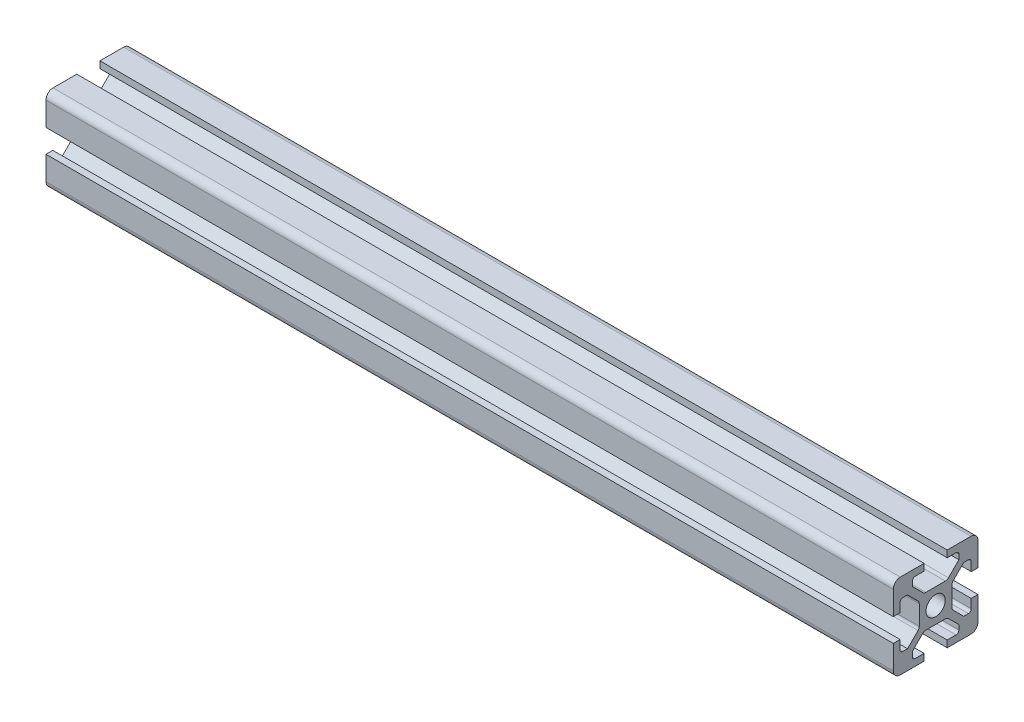
SolidWorks part; units mm, degrees
ref_plane "Front Plane" through (0, 0, 0) normal (0, 0, 1) x (1, 0, 0)
ref_plane "Top Plane" through (0, 0, 0) normal (0, 1, 0) x (1, 0, 0)
ref_plane "Right Plane" through (0, 0, 0) normal (1, 0, 0) x (0, 0, -1)
sketch "Sketch1" plane through (0, 0, 0) normal (1, 0, 0) x (0, 0, -1)
  line L0 (10.9, 0) -> (10.9, 2.4)
  line L1 (0, 0) -> (10.9, 0)
  line L2 (0, 0) -> (0, 10.9)
  line L3 (0, 30) -> (10.9, 30)
  line L4 (30, 0) -> (30, 10.9)
  line L5 (19.1, 0) -> (19.1, 2.4)
  line L6 (0, 10.9) -> (2.4, 10.9)
  line L7 (0, 19.1) -> (2.4, 19.1)
  line L8 (10.9, 30) -> (10.9, 27.6)
  line L9 (19.1, 30) -> (19.1, 27.6)
  line L10 (30, 19.1) -> (27.6, 19.1)
  line L11 (27.6, 10.9) -> (30, 10.9)
  line L12 (24.95, 23.25) -> (27.6, 23.25)
  line L18 (6.75, 2.4) -> (10.9, 2.4)
  line L19 (27.6, 6.75) -> (27.6, 10.9)
  line L20 (2.4, 6.75) -> (2.4, 10.9)
  line L21 (6.75, 27.6) -> (10.9, 27.6)
  line L22 (19.1, 2.4) -> (23.25, 2.4)
  line L23 (27.6, 19.1) -> (27.6, 23.25)
  line L24 (2.4, 19.1) -> (2.4, 23.25)
  line L25 (19.1, 27.6) -> (23.25, 27.6)
  line L26 (19.1, 20.8) -> (10.9, 20.8)
  line L29 (5.05, 6.75) -> (2.4, 6.75)
  line L31 (2.4, 23.25) -> (5.05, 23.25)
  line L34 (6.75, 24.95) -> (6.75, 27.6)
  line L40 (23.25, 2.4) -> (23.25, 5.05)
  line L43 (9.2, 10.9) -> (9.2, 19.1)
  line L44 (19.1, 9.2) -> (10.9, 9.2)
  line L45 (20.8, 10.9) -> (20.8, 19.1)
  line L46 (24.95, 6.75) -> (20.8, 10.9)
  line L47 (19.1, 9.2) -> (23.25, 5.05)
  line L48 (20.8, 19.1) -> (24.95, 23.25)
  line L49 (10.9, 9.2) -> (6.75, 5.05)
  line L50 (5.05, 6.75) -> (9.2, 10.9)
  line L51 (19.1, 20.8) -> (23.25, 24.95)
  line L52 (6.75, 24.95) -> (10.9, 20.8)
  line L53 (5.05, 23.25) -> (9.2, 19.1)
  line L54 (19.1, 30) -> (30, 30)
  line L55 (30, 19.1) -> (30, 30)
  line L56 (19.1, 0) -> (30, 0)
  line L57 (0, 19.1) -> (0, 30)
  line L58 (6.75, 5.05) -> (6.75, 2.4)
  line L59 (24.95, 6.75) -> (27.6, 6.75)
  line L60 (23.25, 27.6) -> (23.25, 24.95)
  circle A0 centre (15, 15) radius 3.4
  point P5 (10.9, 0)
  point P6 (19.1, 0)
  point P7 (0, 10.9)
  point P8 (0, 19.1)
  point P9 (30, 19.1)
  point P10 (30, 10.9)
  point P11 (19.1, 30)
  point P12 (10.9, 30)
  point P59 (15, 20.8)
  point P61 (9.2, 15)
  point P62 (15, 9.2)
  point P65 (20.8, 15)
  point P67 (24.95, 6.75)
  point P70 (15, 20.8)
  point P73 (9.2, 15)
  point P76 (15, 9.2)
  point P79 (20.8, 15)
  point P80 (23.25, 5.05)
  point P81 (24.95, 23.25)
  point P82 (6.75, 5.05)
  point P84 (5.05, 6.75)
  point P88 (23.25, 24.95)
  point P90 (6.75, 24.95)
  point P92 (5.05, 23.25)
extrude "Boss-Extrude2" add sketch "Sketch1" along normal blind 100
fillet "Fillet5" radius 2.5 4 edges at (50, 0, -30) (50, 30, -30) (50, 0, 0) (50, 30, 0)
fillet "Fillet6" radius 1.5 6 edges at (50, 19.1, -20.8) (50, 10.9, -20.8) (50, 9.2, -10.9) (50, 9.2, -19.1) (50, 10.9, -9.2) (50, 19.1, -9.2)
fillet "Fillet7" radius 1.5 2 edges at (50, 20.8, -19.1) (50, 20.8, -10.9)
fillet "Fillet8" radius 1 8 edges at (50, 23.25, -2.4) (50, 27.6, -6.75) (50, 27.6, -23.25) (50, 23.25, -27.6) (50, 6.75, -27.6) (50, 2.4, -23.25) (50, 2.4, -6.75) (50, 6.75, -2.4)
sketch "Sketch3" plane through (0, 0, 0) normal (1, 0, 0) x (0, 0, -1)
  line L0 (10.9, 27.6) -> (10.9, 30) construction
  line L1 (7.75, 27.6) -> (10.9, 27.6) construction
  line L2 (6.75, 24.95) -> (6.75, 26.6) construction
  line L3 (10.4607, 21.2393) -> (6.75, 24.95) construction
  line L4 (18.4787, 20.8) -> (11.5213, 20.8) construction
  line L5 (23.25, 24.95) -> (19.5393, 21.2393) construction
  line L6 (23.25, 26.6) -> (23.25, 24.95) construction
  line L7 (19.1, 27.6) -> (22.25, 27.6) construction
  line L8 (19.1, 30) -> (19.1, 27.6) construction
  line L9 (27.5, 30) -> (19.1, 30) construction
  line L10 (30, 19.1) -> (30, 27.5) construction
  line L11 (27.6, 19.1) -> (30, 19.1) construction
  line L12 (27.6, 22.25) -> (27.6, 19.1) construction
  line L13 (24.95, 23.25) -> (26.6, 23.25) construction
  line L14 (21.2393, 19.5393) -> (24.95, 23.25) construction
  line L15 (20.8, 11.5213) -> (20.8, 18.4787) construction
  line L16 (24.95, 6.75) -> (21.2393, 10.4607) construction
  line L17 (26.6, 6.75) -> (24.95, 6.75) construction
  line L18 (27.6, 10.9) -> (27.6, 7.75) construction
  line L19 (30, 10.9) -> (27.6, 10.9) construction
  line L20 (30, 2.5) -> (30, 10.9) construction
  line L21 (19.1, 0) -> (27.5, 0) construction
  line L22 (19.1, 2.4) -> (19.1, 0) construction
  line L23 (22.25, 2.4) -> (19.1, 2.4) construction
  line L24 (23.25, 5.05) -> (23.25, 3.4) construction
  line L25 (19.5393, 8.7607) -> (23.25, 5.05) construction
  line L26 (11.5213, 9.2) -> (18.4787, 9.2) construction
  line L27 (6.75, 5.05) -> (10.4607, 8.7607) construction
  line L28 (6.75, 3.4) -> (6.75, 5.05) construction
  line L29 (10.9, 2.4) -> (7.75, 2.4) construction
  line L30 (10.9, 0) -> (10.9, 2.4) construction
  line L31 (2.5, 0) -> (10.9, 0) construction
  line L32 (0, 10.9) -> (0, 2.5) construction
  line L33 (2.4, 10.9) -> (0, 10.9) construction
  line L34 (2.4, 7.75) -> (2.4, 10.9) construction
  line L35 (5.05, 6.75) -> (3.4, 6.75) construction
  line L36 (8.7607, 10.4607) -> (5.05, 6.75) construction
  line L37 (9.2, 18.4787) -> (9.2, 11.5213) construction
  line L38 (5.05, 23.25) -> (8.7607, 19.5393) construction
  line L39 (3.4, 23.25) -> (5.05, 23.25) construction
  line L40 (2.4, 19.1) -> (2.4, 22.25) construction
  line L41 (0, 19.1) -> (2.4, 19.1) construction
  line L42 (0, 27.5) -> (0, 19.1) construction
  line L43 (10.9, 30) -> (2.5, 30) construction
  line L44 (10.9, 27.6) -> (10.9, 30)
  line L45 (7.75, 27.6) -> (10.9, 27.6)
  line L46 (6.75, 24.95) -> (6.75, 26.6)
  line L47 (10.4607, 21.2393) -> (6.75, 24.95)
  line L48 (18.4787, 20.8) -> (11.5213, 20.8)
  line L49 (23.25, 24.95) -> (19.5393, 21.2393)
  line L50 (23.25, 26.6) -> (23.25, 24.95)
  line L51 (19.1, 27.6) -> (22.25, 27.6)
  line L52 (19.1, 30) -> (19.1, 27.6)
  line L53 (27.5, 30) -> (19.1, 30)
  line L54 (30, 19.1) -> (30, 27.5)
  line L55 (27.6, 19.1) -> (30, 19.1)
  line L56 (27.6, 22.25) -> (27.6, 19.1)
  line L57 (24.95, 23.25) -> (26.6, 23.25)
  line L58 (21.2393, 19.5393) -> (24.95, 23.25)
  line L59 (20.8, 11.5213) -> (20.8, 18.4787)
  line L60 (24.95, 6.75) -> (21.2393, 10.4607)
  line L61 (26.6, 6.75) -> (24.95, 6.75)
  line L62 (27.6, 10.9) -> (27.6, 7.75)
  line L63 (30, 10.9) -> (27.6, 10.9)
  line L64 (30, 2.5) -> (30, 10.9)
  line L65 (19.1, 0) -> (27.5, 0)
  line L66 (19.1, 2.4) -> (19.1, 0)
  line L67 (22.25, 2.4) -> (19.1, 2.4)
  line L68 (23.25, 5.05) -> (23.25, 3.4)
  line L69 (19.5393, 8.7607) -> (23.25, 5.05)
  line L70 (11.5213, 9.2) -> (18.4787, 9.2)
  line L71 (6.75, 5.05) -> (10.4607, 8.7607)
  line L72 (6.75, 3.4) -> (6.75, 5.05)
  line L73 (10.9, 2.4) -> (7.75, 2.4)
  line L74 (10.9, 0) -> (10.9, 2.4)
  line L75 (2.5, 0) -> (10.9, 0)
  line L76 (0, 10.9) -> (0, 2.5)
  line L77 (2.4, 10.9) -> (0, 10.9)
  line L78 (2.4, 7.75) -> (2.4, 10.9)
  line L79 (5.05, 6.75) -> (3.4, 6.75)
  line L80 (8.7607, 10.4607) -> (5.05, 6.75)
  line L81 (9.2, 18.4787) -> (9.2, 11.5213)
  line L82 (5.05, 23.25) -> (8.7607, 19.5393)
  line L83 (3.4, 23.25) -> (5.05, 23.25)
  line L84 (2.4, 19.1) -> (2.4, 22.25)
  line L85 (0, 19.1) -> (2.4, 19.1)
  line L86 (0, 27.5) -> (0, 19.1)
  line L87 (10.9, 30) -> (2.5, 30)
  circle A0 centre (15, 15) radius 3.4 construction
  arc A1 (7.75, 27.6) -> (6.75, 26.6) centre (7.75, 26.6) ccw construction
  arc A2 (10.4607, 21.2393) -> (11.5213, 20.8) centre (11.5213, 22.3) ccw construction
  arc A3 (18.4787, 20.8) -> (19.5393, 21.2393) centre (18.4787, 22.3) ccw construction
  arc A4 (23.25, 26.6) -> (22.25, 27.6) centre (22.25, 26.6) ccw construction
  arc A5 (30, 27.5) -> (27.5, 30) centre (27.5, 27.5) ccw construction
  arc A6 (27.6, 22.25) -> (26.6, 23.25) centre (26.6, 22.25) ccw construction
  arc A7 (21.2393, 19.5393) -> (20.8, 18.4787) centre (22.3, 18.4787) ccw construction
  arc A8 (20.8, 11.5213) -> (21.2393, 10.4607) centre (22.3, 11.5213) ccw construction
  arc A9 (26.6, 6.75) -> (27.6, 7.75) centre (26.6, 7.75) ccw construction
  arc A10 (27.5, 0) -> (30, 2.5) centre (27.5, 2.5) ccw construction
  arc A11 (22.25, 2.4) -> (23.25, 3.4) centre (22.25, 3.4) ccw construction
  arc A12 (19.5393, 8.7607) -> (18.4787, 9.2) centre (18.4787, 7.7) ccw construction
  arc A13 (11.5213, 9.2) -> (10.4607, 8.7607) centre (11.5213, 7.7) ccw construction
  arc A14 (6.75, 3.4) -> (7.75, 2.4) centre (7.75, 3.4) ccw construction
  arc A15 (0, 2.5) -> (2.5, 0) centre (2.5, 2.5) ccw construction
  arc A16 (2.4, 7.75) -> (3.4, 6.75) centre (3.4, 7.75) ccw construction
  arc A17 (9.2, 18.4787) -> (8.7607, 19.5393) centre (7.7, 18.4787) ccw construction
  arc A18 (8.7607, 10.4607) -> (9.2, 11.5213) centre (7.7, 11.5213) ccw construction
  arc A19 (3.4, 23.25) -> (2.4, 22.25) centre (3.4, 22.25) ccw construction
  arc A20 (2.5, 30) -> (0, 27.5) centre (2.5, 27.5) ccw construction
  circle A21 centre (15, 15) radius 3.4
  arc A22 (7.75, 27.6) -> (6.75, 26.6) centre (7.75, 26.6) ccw
  arc A23 (10.4607, 21.2393) -> (11.5213, 20.8) centre (11.5213, 22.3) ccw
  arc A24 (18.4787, 20.8) -> (19.5393, 21.2393) centre (18.4787, 22.3) ccw
  arc A25 (23.25, 26.6) -> (22.25, 27.6) centre (22.25, 26.6) ccw
  arc A26 (30, 27.5) -> (27.5, 30) centre (27.5, 27.5) ccw
  arc A27 (27.6, 22.25) -> (26.6, 23.25) centre (26.6, 22.25) ccw
  arc A28 (21.2393, 19.5393) -> (20.8, 18.4787) centre (22.3, 18.4787) ccw
  arc A29 (20.8, 11.5213) -> (21.2393, 10.4607) centre (22.3, 11.5213) ccw
  arc A30 (26.6, 6.75) -> (27.6, 7.75) centre (26.6, 7.75) ccw
  arc A31 (27.5, 0) -> (30, 2.5) centre (27.5, 2.5) ccw
  arc A32 (22.25, 2.4) -> (23.25, 3.4) centre (22.25, 3.4) ccw
  arc A33 (19.5393, 8.7607) -> (18.4787, 9.2) centre (18.4787, 7.7) ccw
  arc A34 (11.5213, 9.2) -> (10.4607, 8.7607) centre (11.5213, 7.7) ccw
  arc A35 (6.75, 3.4) -> (7.75, 2.4) centre (7.75, 3.4) ccw
  arc A36 (0, 2.5) -> (2.5, 0) centre (2.5, 2.5) ccw
  arc A37 (2.4, 7.75) -> (3.4, 6.75) centre (3.4, 7.75) ccw
  arc A38 (9.2, 18.4787) -> (8.7607, 19.5393) centre (7.7, 18.4787) ccw
  arc A39 (8.7607, 10.4607) -> (9.2, 11.5213) centre (7.7, 11.5213) ccw
  arc A40 (3.4, 23.25) -> (2.4, 22.25) centre (3.4, 22.25) ccw
  arc A41 (2.5, 30) -> (0, 27.5) centre (2.5, 27.5) ccw
extrude "Boss-Extrude4" add sketch "Sketch3" against normal blind 200
